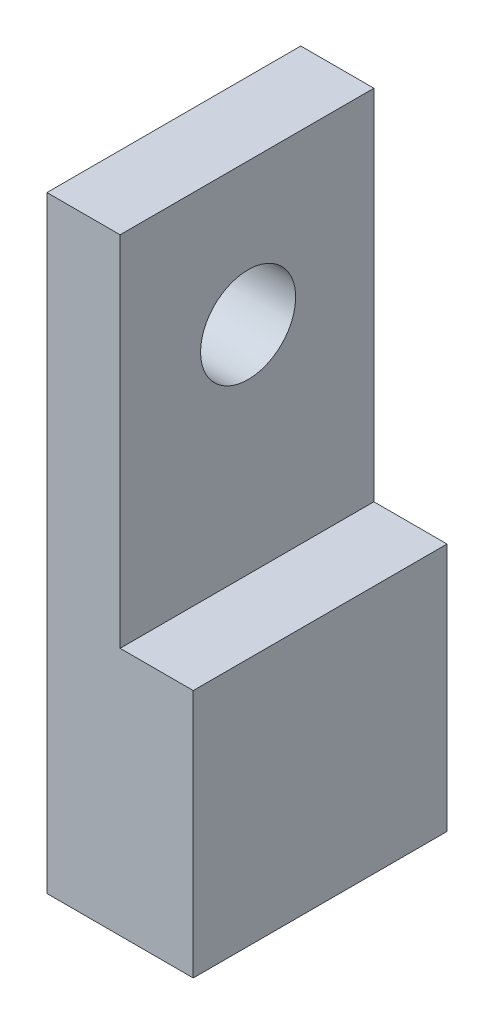
SolidWorks part; units mm, degrees
material "6061-T6 (SS)"
ref_plane "Front Plane" through (0, 0, 0) normal (0, 0, 1) x (1, 0, 0)
ref_plane "Top Plane" through (0, 0, 0) normal (0, 1, 0) x (1, 0, 0)
ref_plane "Right Plane" through (0, 0, 0) normal (1, 0, 0) x (0, 0, -1)
sketch "Sketch1" plane through (0, 0, 0) normal (0, 1, 0) x (1, 0, 0)
  line L1 (-4.3431, 11.7969) -> (15.6569, 11.7969)
  line L2 (-4.3431, 11.7969) -> (-4.3431, -22.9031)
  line L3 (-4.3431, -22.9031) -> (15.6569, -22.9031)
  line L4 (15.6569, 11.7969) -> (15.6569, -22.9031)
  line L5 (-4.3431, 11.7969) -> (15.6569, -22.9031) construction
  line L6 (-4.3431, -22.9031) -> (15.6569, 11.7969) construction
  point P4 (5.6569, -5.5531)
  dimension "D1" = 20
  dimension "D2" = 34.7
extrude "Boss-Extrude1" add sketch "Sketch1" along normal blind 83
sketch "Sketch3" plane through (0, 0, -11.7969) normal (0, 0, -1) x (-1, 0, 0)
  line L0 (-15.6569, 83) -> (4.3431, 83) construction
  line L1 (-5.6569, 83) -> (-15.6569, 83)
  line L2 (-5.6569, 83) -> (-5.6569, 34.035)
  line L3 (-5.6569, 34.035) -> (-15.6569, 34.035)
  line L4 (-15.6569, 83) -> (-15.6569, 34.035)
  line L5 (-5.6569, 83) -> (-15.6569, 34.035) construction
  line L6 (-5.6569, 34.035) -> (-15.6569, 83) construction
  line L7 (-15.6569, 83) -> (-15.6569, 0) construction
  point P4 (-10.6569, 58.5175)
extrude "Cut-Extrude2" cut sketch "Sketch3" against normal up to next
sketch "Sketch4" plane through (-4.3431, 0, 0) normal (-1, 0, 0) x (0, 0, 1)
  circle A0 centre (5.4031, 63.6096) radius 6.5
extrude "Cut-Extrude3" cut sketch "Sketch4" against normal up to next
hole_wizard "M3x0.5 Tapped Hole1" positions "Sketch5" profile "Sketch6" tap size "M3x0.5" standard "ANSI Metric"
sketch "Sketch5" plane through (-4.3431, 0, 0) normal (-1, 0, 0) x (0, 0, 1)
  circle A0 centre (5.4031, 63.6096) radius 6.5 construction
  point P0 (-7.0969, 51.1096)
  point P3 (17.9031, 51.1096)
  point P6 (17.9031, 76.1096)
  point P9 (-7.0969, 76.1096)
  point P12 (0, 0)
  point P13 (0, 0)
  point P14 (0, 0)
  point P15 (0, 0)
  point P16 (0, 0)
  point P17 (0, 0)
  point P18 (0, 0)
  point P19 (0, 0)
  dimension "D1" = 25
  dimension "D2" = 25
  dimension "D3" = 12.5
  dimension "D4" = 12.5
sketch "Sketch6" plane through (-4.3431, 51.1096, -7.0969) normal (0, 1, 0) x (0, 0, 1)
  line L0 (0, 0) -> (0, 8.2511)
  line L1 (0, 8.2511) -> (1.25, 7.5)
  line L2 (1.25, 7.5) -> (1.25, 0)
  line L5 (1.25, 0) -> (0, 0)
  line L10 (0, 8.2511) -> (-1.25, 7.5) construction
  line L11 (0, -6.35) -> (0, 107.95) construction
  dimension "Tap Drill Dia." = 2.5
  dimension "Tap Drill Depth" = 7.5
  dimension "Drill Angle" = 118
cosmetic thread "Hole Thread1" parameters "D1"=6, "D2"=3
cosmetic thread "Hole Thread2" parameters "D1"=6, "D2"=3
cosmetic thread "Hole Thread3" parameters "D1"=6, "D2"=3
cosmetic thread "Hole Thread4" parameters "D1"=6, "D2"=3
hole_wizard "M6x1.0 Tapped Hole1" positions "Sketch10" profile "Sketch11" tap size "M6x1.0" standard "ANSI Metric"
sketch "Sketch10" plane through (0, 0, 0) normal (0, -1, 0) x (-1, 0, 0)
  point P0 (-5.6569, -5.5531)
sketch "Sketch11" plane through (5.6569, 0, 5.5531) normal (1, 0, 0) x (0, 0, -1)
  line L0 (0, 0) -> (0, 16.5022)
  line L1 (0, 16.5022) -> (2.5, 15)
  line L2 (2.5, 15) -> (2.5, 0)
  line L5 (2.5, 0) -> (0, 0)
  line L10 (0, 16.5022) -> (-2.5, 15) construction
  line L11 (0, -6.35) -> (0, 107.95) construction
  dimension "Tap Drill Dia." = 5
  dimension "Tap Drill Depth" = 15
  dimension "Drill Angle" = 118
cosmetic thread "Hole Thread5" parameters "D1"=12, "D2"=6
hole_wizard "Ø4.0mm Dowel Hole1" positions "Sketch12" profile "Sketch13" hole size "Ø4.0" standard "ANSI Metric"
sketch "Sketch12" plane through (0, 0, 0) normal (0, -1, 0) x (-1, 0, 0)
  line L0 (4.3431, -22.9031) -> (-15.6569, -22.9031) construction
  line L1 (-15.6569, 11.7969) -> (4.3431, 11.7969) construction
  point P0 (-5.6569, -17.9031)
  point P2 (-5.6569, 6.7969)
  dimension "D1" = 5
  dimension "D2" = 5
sketch "Sketch13" plane through (5.6569, 0, 17.9031) normal (1, 0, 0) x (0, 0, -1)
  line L0 (0, 0) -> (0, 6.4017)
  line L1 (0, 6.4017) -> (2, 5.2)
  line L2 (2, 5.2) -> (2, 0)
  line L5 (2, 0) -> (0, 0)
  line L10 (0, 6.4017) -> (-2, 5.2) construction
  line L11 (0, -6.35) -> (0, 107.95) construction
  dimension "Hole Dia." = 4
  dimension "Hole Depth" = 5.2
  dimension "Drill Angle" = 118
